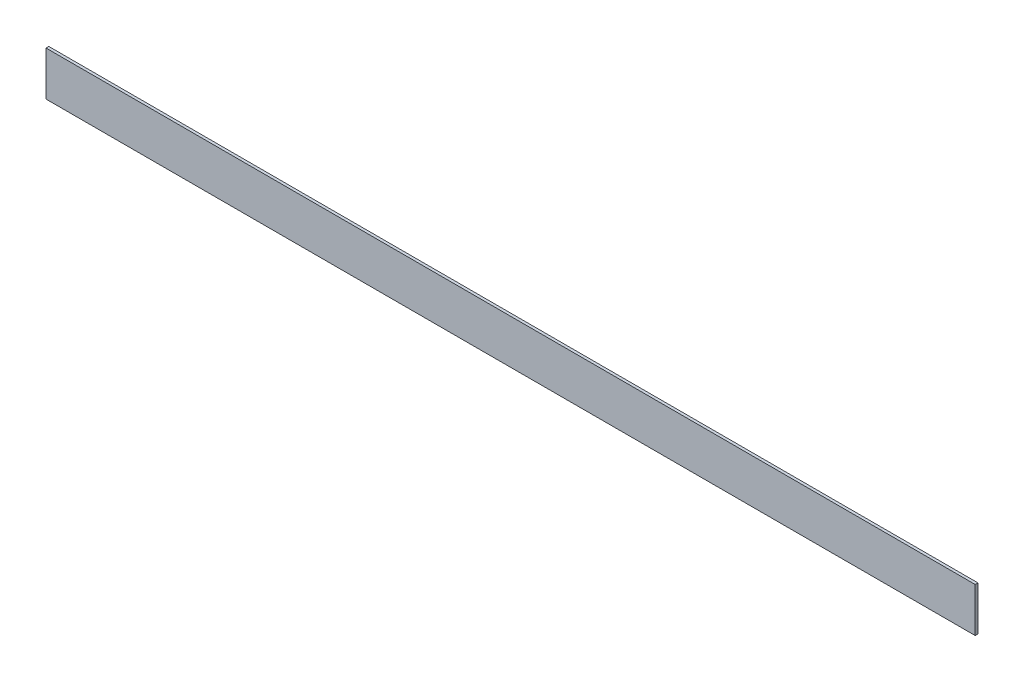
SolidWorks part; units mm, degrees
material "Nylon 101"
ref_plane "Front Plane" through (0, 0, 0) normal (0, 0, 1) x (1, 0, 0)
ref_plane "Top Plane" through (0, 0, 0) normal (0, 1, 0) x (1, 0, 0)
ref_plane "Right Plane" through (0, 0, 0) normal (1, 0, 0) x (0, 0, -1)
sketch "Sketch1" plane through (0, 0, 0) normal (0, 0, 1) x (1, 0, 0)
  line L1 (-128.864, 114.2874) -> (404.536, 114.2874)
  line L2 (-128.864, 114.2874) -> (-128.864, 88.8874)
  line L3 (-128.864, 88.8874) -> (404.536, 88.8874)
  line L4 (404.536, 114.2874) -> (404.536, 88.8874)
  dimension "D1" = 533.4
  dimension "D2" = 25.4
extrude "Boss-Extrude1" add sketch "Sketch1" along normal blind 1.5875
